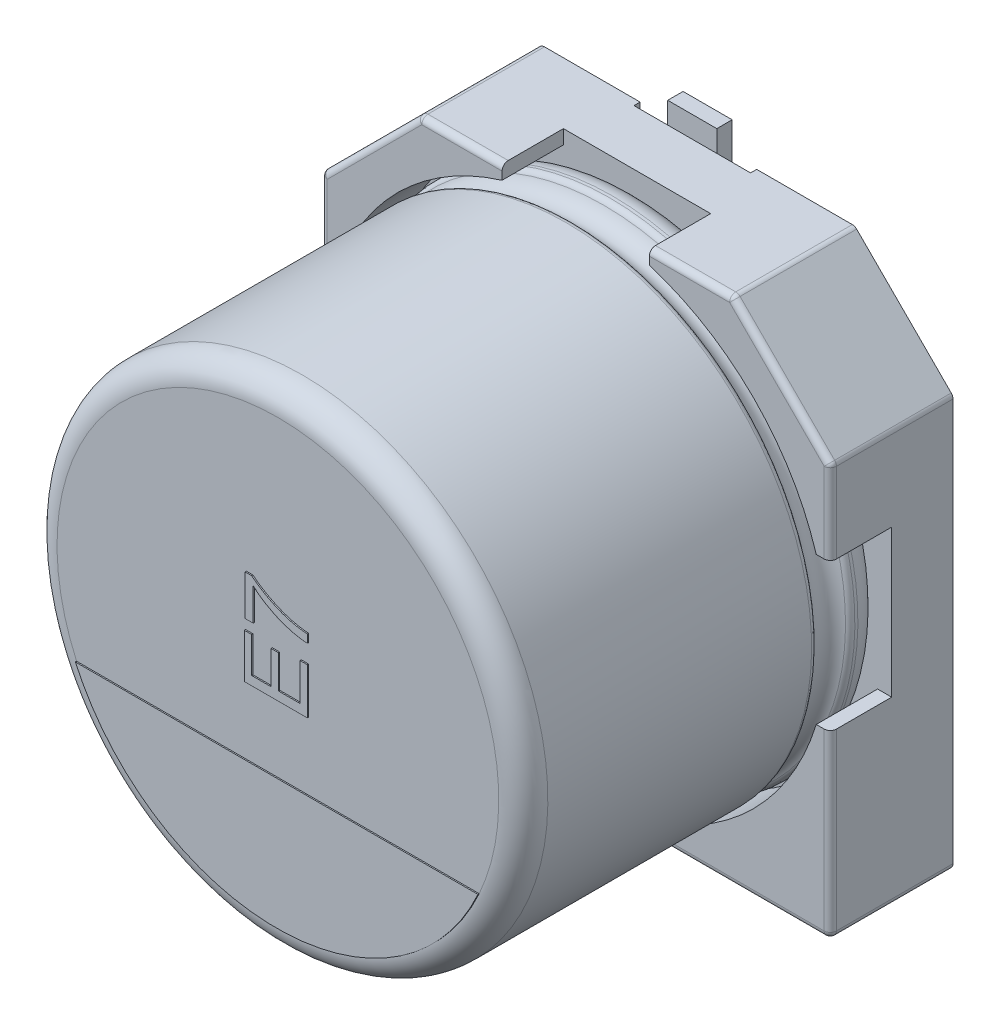
SolidWorks part; units mm, degrees
ref_plane "Plan de face" through (0, 0, 0) normal (0, 0, 1) x (1, 0, 0)
ref_plane "Plan de dessus" through (0, 0, 0) normal (0, 1, 0) x (1, 0, 0)
ref_plane "Plan de droite" through (0, 0, 0) normal (1, 0, 0) x (0, 0, -1)
sketch "Sketch2" plane through (0, 0, 0) normal (0, 0, 1) x (1, 0, 0)
  line L0 (-4.15, 2.55) -> (-2.55, 4.15)
  line L1 (-2.55, 4.15) -> (2.55, 4.15)
  line L2 (-4.15, 2.55) -> (-4.15, -4.15)
  line L3 (-4.15, -4.15) -> (4.15, -4.15)
  line L4 (4.15, 2.55) -> (4.15, -4.15)
  line L5 (-4.15, 4.15) -> (4.15, -4.15) construction
  line L6 (-4.15, -4.15) -> (4.15, 4.15) construction
  line L7 (2.55, 4.15) -> (4.15, 2.55)
  point P0 (0, 0)
  dimension "D1" = 8.3
  dimension "D2" = 8.3
extrude "Boss-Extrude1" add sketch "Sketch2" along normal blind 1
sketch "Sketch4" plane through (0, 0, 1) normal (0, 0, 1) x (1, 0, 0)
  line L0 (-4.15, 2.55) -> (-2.55, 4.15)
  line L1 (-2.55, 4.15) -> (-1.2, 4.15)
  line L3 (-4.15, 1.2) -> (-4.15, 2.55)
  line L4 (2.55, 4.15) -> (4.15, 2.55)
  line L5 (4.15, 2.55) -> (4.15, 1.2)
  line L6 (4.15, -4.15) -> (4.15, 2.55) construction
  line L7 (2.55, 4.15) -> (-2.55, 4.15) construction
  line L8 (1.2, 4.15) -> (2.55, 4.15)
  line L9 (-4.15, -4.15) -> (4.15, -4.15) construction
  line L10 (4.15, -1.2) -> (4.15, -4.15)
  line L11 (4.15, -4.15) -> (1.2, -4.15)
  line L12 (-4.15, -1.2) -> (-4.15, -4.15)
  line L13 (-4.15, -4.15) -> (-1.2, -4.15)
  line L14 (-4.946, -1.2) -> (4.946, -1.2) construction
  line L15 (-4.8253, 1.2) -> (5.0249, 1.2) construction
  line L16 (3.9205, 1.2) -> (4.15, 1.2)
  line L17 (3.9205, -1.2) -> (4.15, -1.2)
  line L18 (-3.9205, -1.2) -> (-4.15, -1.2)
  line L19 (-3.9205, 1.2) -> (-4.15, 1.2)
  line L20 (-1.2, 5.0139) -> (-1.2, -5.2906) construction
  line L21 (1.2, 5.0139) -> (1.2, -5.4) construction
  line L22 (-1.2, 4.15) -> (-1.2, 3.9205)
  line L23 (1.2, 4.15) -> (1.2, 3.9205)
  line L24 (-1.2, -3.9205) -> (-1.2, -4.15)
  line L25 (1.2, -3.9205) -> (1.2, -4.15)
  arc A0 (-1.2, 3.9205) -> (-3.9205, 1.2) centre (0, 0) ccw construction
  arc A1 (-3.9205, 1.2) -> (-1.2, 3.9205) centre (0, 0) cw
  arc A2 (1.2, 3.9205) -> (3.9205, 1.2) centre (0, 0) cw
  arc A3 (1.2, -3.9205) -> (3.9205, -1.2) centre (0, 0) ccw
  arc A4 (-1.2, -3.9205) -> (-3.9205, -1.2) centre (0, 0) cw
  arc A5 (3.9205, 1.2) -> (1.2, 3.9205) centre (0, 0) ccw construction
  arc A6 (1.2, -3.9205) -> (3.9205, -1.2) centre (0, 0) ccw construction
  arc A7 (-3.9205, -1.2) -> (-1.2, -3.9205) centre (0, 0) ccw construction
  point P33 (0, -1.2)
  dimension "D1" = 8.2
  dimension "D2" = 1.2
  dimension "D3" = 1.2
  dimension "D4" = 1.2
  dimension "D5" = 1.2
sketch "Sketch5" plane through (0, 0, 0) normal (0, 0, 1) x (1, 0, 0)
extrude "Boss-Extrude2" add sketch "Sketch4" along normal blind 1
sketch "Sketch7" plane through (0, 0, 0) normal (0, 0, -1) x (1, 0, 0)
  line L1 (-2.9065, 2.8449) -> (2.9065, 2.8449) construction
  line L2 (-2.9065, 2.8449) -> (-2.9065, -2.8449) construction
  line L3 (-2.9065, -2.8449) -> (2.9065, -2.8449) construction
  line L4 (2.9065, 2.8449) -> (2.9065, -2.8449) construction
  line L5 (-2.9065, 2.8449) -> (2.9065, -2.8449) construction
  line L6 (-2.9065, -2.8449) -> (2.9065, 2.8449) construction
  circle A0 centre (-2.9065, 2.8449) radius 0.35
  circle A1 centre (2.9065, 2.8449) radius 0.35
  circle A2 centre (-2.9065, -2.8449) radius 0.35
  circle A3 centre (2.9065, -2.8449) radius 0.35
  point P0 (0, 0)
  dimension "D1" = 0.7
  dimension "D2" = 0.7
  dimension "D3" = 0.7
  dimension "D4" = 0.7
extrude "Spacer Pad" add sketch "Sketch7" along normal blind 0.15
sketch "Sketch8" plane through (0, 0, 0) normal (0, 0, -1) x (1, 0, 0)
  line L0 (-0.95, 4.3618) -> (-0.95, -4.4479) construction
  line L1 (0.95, 4.3618) -> (0.95, -4.4479) construction
  dimension "D1" = 0.95
  dimension "D2" = 1.9
sketch "Sketch9" plane through (0, 0, 0) normal (0, 0, -1) x (1, 0, 0)
  line L0 (-4.6239, -1.5) -> (5.0007, -1.5) construction
  line L1 (-4.6239, 1.5) -> (5.2975, 1.5) construction
  line L2 (-0.95, 4.3618) -> (-0.95, -4.4479) construction
  line L3 (-0.95, 1.5) -> (0.95, 1.5)
  line L4 (-0.95, 1.5) -> (-0.95, 4.15)
  line L5 (-0.95, 4.15) -> (0.95, 4.15)
  line L6 (0.95, 1.5) -> (0.95, 4.15)
  line L7 (0.95, 4.3618) -> (0.95, -4.4479) construction
  line L8 (-4.15, 4.15) -> (4.15, 4.15) construction
  line L9 (2.55, -4.15) -> (-2.55, -4.15) construction
  line L10 (-0.95, -1.5) -> (0.95, -1.5)
  line L11 (-0.95, -1.5) -> (-0.95, -4.15)
  line L12 (-0.95, -4.15) -> (0.95, -4.15)
  line L13 (0.95, -1.5) -> (0.95, -4.15)
  dimension "D1" = 1.5
  dimension "D2" = 1.5
extrude "Cut-Extrude1" cut sketch "Sketch9" against normal blind 0.1
fillet "Fillet1" radius 0.1 6 edges at (-4.15, 2.55, 1) (-2.55, 4.15, 1) (2.55, 4.15, 1) (4.15, 2.55, 1) (4.15, -4.15, 1) (-4.15, -4.15, 1)
sketch "Sketch10" plane through (0, 0, 0) normal (1, 0, 0) x (0, 0, -1)
  line L0 (18.9631, 0) -> (-18.9631, 0) construction
  line L2 (-6.8536, 0) -> (-6.8536, 3.6)
  line L3 (-6.4536, 4) -> (-2.1546, 4)
  line L4 (-1, 3.6) -> (-1, 0)
  line L7 (-1.4494, 4) -> (-1.4, 4)
  arc A0 (-6.8536, 3.6) -> (-6.4536, 4) centre (-6.4536, 3.6) cw
  arc A1 (-1.4, 4) -> (-1, 3.6) centre (-1.4, 3.6) cw
  arc A2 (-1.5413, 3.9394) -> (-2.0626, 3.9394) centre (-1.802, 4.051) cw
  arc A3 (-2.0626, 3.9394) -> (-2.1546, 4) centre (-2.1546, 3.9) ccw
  arc A4 (-1.5413, 3.9394) -> (-1.4494, 4) centre (-1.4494, 3.9) cw
  point P4 (0, 0)
  point P13 (-6.8536, 4)
  dimension "D2" = 0.4
  dimension "D3" = 0.4
  dimension "D4" = 0.1
  dimension "D5" = 0.1
  dimension "D1" = 4
revolve "Revolve1" add sketch "Sketch10" angle 360 about L0
fillet "Fillet2" radius 0.1 16 edges at (2.625, -4.15, 2) (4.1207, -4.1207, 2) (4.15, 1.8543, 2) (4.1424, 2.5468, 2) (1.8543, 4.15, 2) (2.5468, 4.1424, 2) (-1.8543, 4.15, 2) (-2.5468, 4.1424, 2) (-3.35, 3.35, 2) (-4.1424, 2.5468, 2) (-4.15, -2.625, 2) (-4.1207, -4.1207, 2) (4.15, -2.625, 2) (3.35, 3.35, 2) (-4.15, 1.8543, 2) (-2.625, -4.15, 2)
sketch "Sketch13" plane through (0, 0, 6.8536) normal (0, 0, 1) x (1, 0, 0)
  line L0 (-5.2631, -1.4818) -> (3.7173, -1.4818) construction
  line L1 (-3.2809, -1.4818) -> (3.2809, -1.4818)
  arc A0 (3.2809, -1.4818) -> (-3.2809, -1.4818) centre (0, 0) cw
  point P3 (-0.7729, -1.4818)
extrude "Cathode marker" add sketch "Sketch13" along normal blind 0.02
sketch "Sketch15" plane through (0, 0, 6.8536) normal (0, 0, 1) x (1, 0, 0)
  line L1 (0.5, 2.1812) -> (0.5, -0.5) construction
  text T1 "E7" font "Arial" height in points 4
extrude "Text" add sketch "Sketch15" along normal blind 0.02
sketch "Sketch18" plane through (0, 0, 0.1) normal (0, 0, -1) x (1, 0, 0)
  line L0 (0, 5.1012) -> (0, -5.1012) construction
  point P4 (0, 0)
sketch "Sketch19" plane through (0, 0, 0.1) normal (0, 0, -1) x (1, 0, 0)
  line L0 (-1.0534, -4.5) -> (1.0534, -4.5) construction
  line L2 (-0.95, -4.15) -> (0.95, -4.15) construction
  line L3 (-1.9391, 4.5) -> (1.9391, 4.5) construction
  line L5 (0.95, 4.15) -> (-0.95, 4.15) construction
  line L6 (0, 5.1012) -> (0, -5.1012) construction
  line L7 (-0.4, 1.6) -> (0.4, 1.6)
  line L8 (-0.4, 1.6) -> (-0.4, 4.5)
  line L9 (-0.4, 4.5) -> (0.4, 4.5)
  line L10 (0.4, 1.6) -> (0.4, 4.5)
  line L11 (-0.4, 1.6) -> (0.4, 4.5) construction
  line L12 (-0.4, 4.5) -> (0.4, 1.6) construction
  line L14 (-0.4, -1.6) -> (0.4, -1.6)
  line L15 (-0.4, -1.6) -> (-0.4, -4.5)
  line L16 (-0.4, -4.5) -> (0.4, -4.5)
  line L17 (0.4, -1.6) -> (0.4, -4.5)
  line L18 (-0.4, -1.6) -> (0.4, -4.5) construction
  line L19 (-0.4, -4.5) -> (0.4, -1.6) construction
  point P3 (0, -4.5)
  point P8 (0, 4.5)
  point P10 (0, 3.05)
  point P17 (0, -3.05)
  dimension "D1" = 0.35
  dimension "D2" = 0.35
  dimension "D3" = 0.8
  dimension "D4" = 2.9
  dimension "D5" = 0.8
  dimension "D6" = 2.9
extrude "Boss-Extrude6" add sketch "Sketch19" along normal blind 0.25
